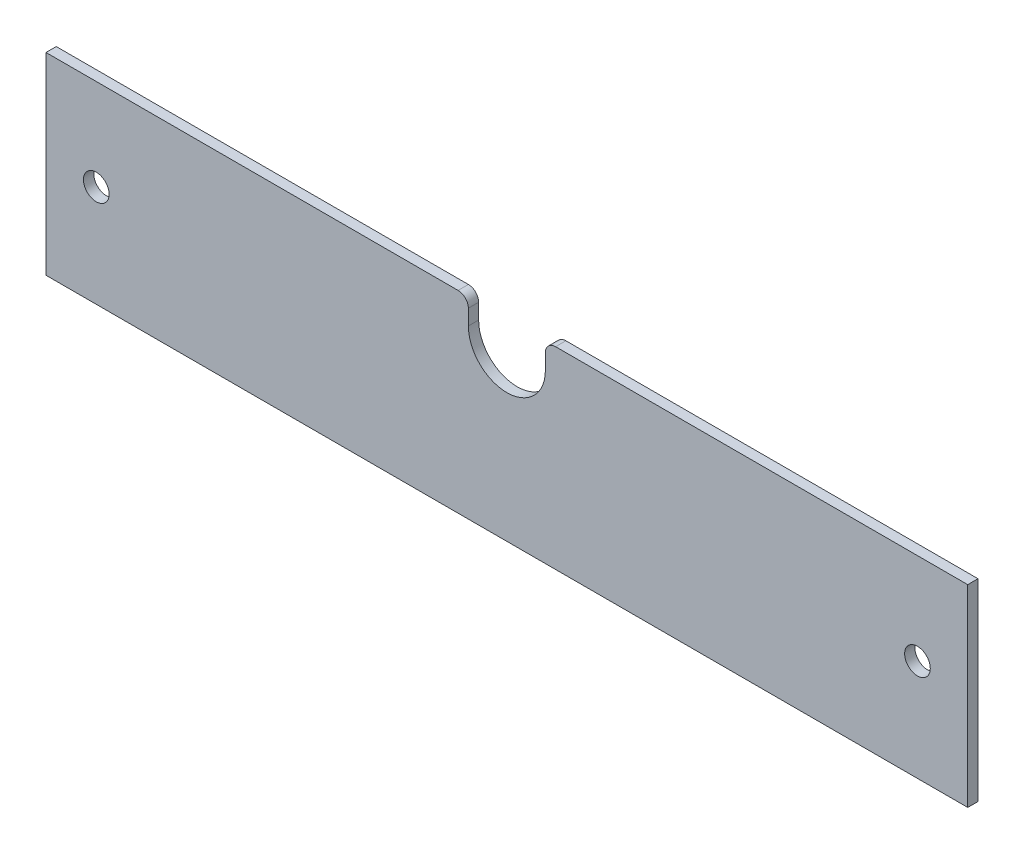
SolidWorks part; units mm, degrees
ref_plane "Plan de face" through (0, 0, 0) normal (0, 0, 1) x (1, 0, 0)
ref_plane "Plan de dessus" through (0, 0, 0) normal (0, 1, 0) x (1, 0, 0)
ref_plane "Plan de droite" through (0, 0, 0) normal (1, 0, 0) x (0, 0, -1)
sketch "Esquisse1" plane through (0, 0, 0) normal (0, 0, 1) x (1, 0, 0)
  line L0 (0, 0) -> (0, 50000) construction
  line L1 (-89.8, -18.8) -> (89.8, -18.8)
  line L2 (-89.8, -18.8) -> (-89.8, 18.8)
  line L3 (-89.8, 18.8) -> (89.8, 18.8)
  line L4 (89.8, -18.8) -> (89.8, 18.8)
  line L5 (-89.8, -18.8) -> (89.8, 18.8) construction
  line L6 (-89.8, 18.8) -> (89.8, -18.8) construction
  line L7 (-7.5, 18.8) -> (7.5, 18.8)
  line L8 (-7.5, 18.8) -> (-7.5, 13.8)
  line L9 (7.5, 18.8) -> (7.5, 13.8)
  circle A0 centre (-80, 1) radius 2.5
  circle A1 centre (80, 1) radius 2.5
  arc A2 (-7.5, 13.8) -> (7.5, 13.8) centre (0, 13.8) ccw
  circle A3 centre (-80, 1) radius 4.5
  circle A4 centre (80, 1) radius 4.5
  point P0 (0, 0)
  point P14 (0, 18.8)
  dimension "D5" = 5
  dimension "D7" = 7.5
  dimension "D1" = 37.6
  dimension "D2" = 179.6
  dimension "D3" = 19.8
  dimension "D4" = 9.8
  dimension "D6" = 15
  dimension "D8" = 5
  dimension "D9" = 2
extrude "Boss.-Extru.1" add sketch "Esquisse1" along normal blind 2 contours A2 L8 L3 L2 L1 L4 L9 A0 A1 | A3 A0 | A4 A1
fillet "Congé1" radius 2 2 edges at (-7.5, 18.8, 1) (7.5, 18.8, 1)
